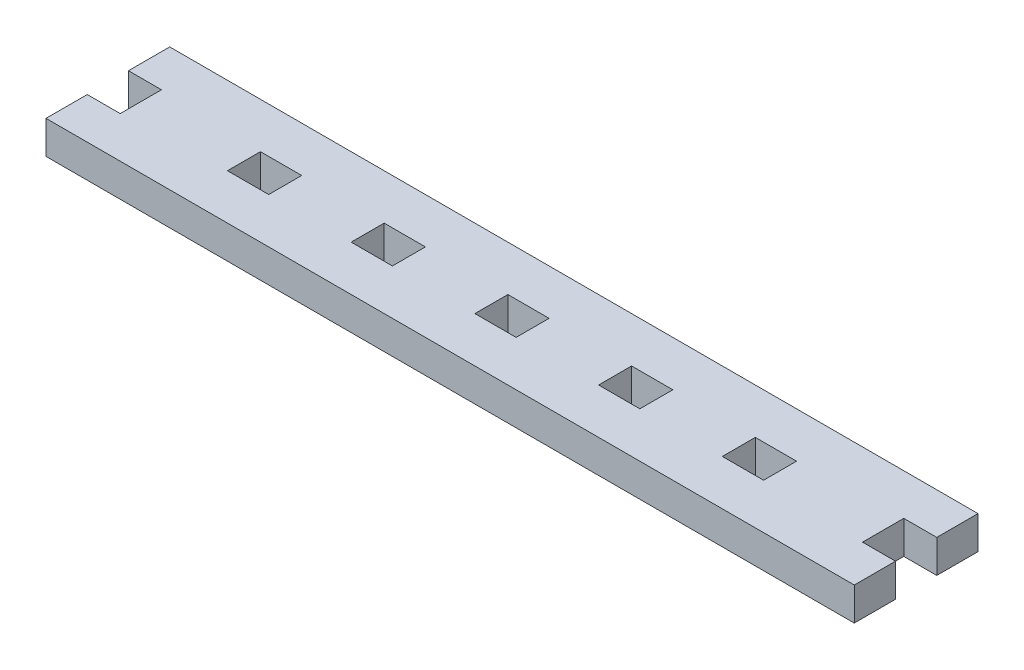
SolidWorks part; units mm, degrees
ref_plane "Front Plane" through (0, 0, 0) normal (0, 0, 1) x (1, 0, 0)
ref_plane "Top Plane" through (0, 0, 0) normal (0, 1, 0) x (1, 0, 0)
ref_plane "Right Plane" through (0, 0, 0) normal (1, 0, 0) x (0, 0, -1)
sketch "Sketch1" plane through (0, 0, 0) normal (0, 1, 0) x (1, 0, 0)
  line L0 (0, 12.7) -> (0, 19.05)
  line L1 (0, 0) -> (124.46, 0)
  line L2 (0, 0) -> (0, 6.35)
  line L3 (0, 19.05) -> (124.46, 19.05)
  line L4 (124.46, 0) -> (124.46, 6.35)
  line L5 (0, 12.7) -> (5.08, 12.7)
  line L7 (0, 6.35) -> (5.08, 6.35)
  line L8 (5.08, 12.7) -> (5.08, 6.35)
  line L9 (124.46, 12.7) -> (119.38, 12.7)
  line L11 (124.46, 6.35) -> (119.38, 6.35)
  line L12 (119.38, 12.7) -> (119.38, 6.35)
  line L13 (124.46, 12.7) -> (124.46, 19.05)
  dimension "D1" = 19.05
  dimension "D2" = 124.46
  dimension "D3" = 6.35
  dimension "D4" = 6.35
  dimension "D5" = 5.08
extrude "Boss-Extrude1" add sketch "Sketch1" along normal blind 5.08
sketch "Sketch2" plane through (0, 5.08, 0) normal (0, 1, 0) x (1, 0, 0)
  line L0 (5.08, 12.7) -> (5.08, 6.35) construction
  line L1 (20.955, 12.065) -> (27.305, 12.065)
  line L2 (20.955, 12.065) -> (20.955, 6.985)
  line L3 (20.955, 6.985) -> (27.305, 6.985)
  line L4 (27.305, 12.065) -> (27.305, 6.985)
  point P6 (20.955, 9.525)
  point P9 (5.08, 9.525)
  dimension "D1" = 5.08
  dimension "D2" = 6.35
  dimension "D3" = 15.875
extrude "Cut-Extrude1" cut sketch "Sketch2" against normal through all
pattern_linear "LPattern1" count 5 spacing 19.05 along (1, 0, 0) of "Cut-Extrude1"
